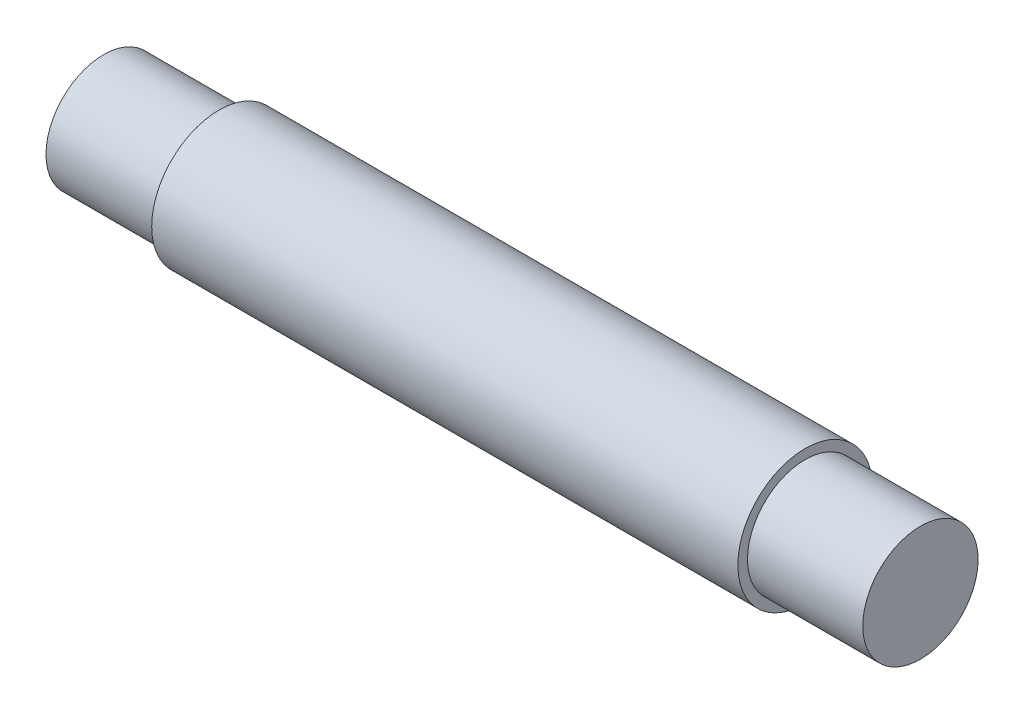
SolidWorks part; units mm, degrees
material "镀铬不锈钢"
ref_plane "前视基准面" through (0, 0, 0) normal (0, 0, 1) x (1, 0, 0)
ref_plane "上视基准面" through (0, 0, 0) normal (0, 1, 0) x (1, 0, 0)
ref_plane "右视基准面" through (0, 0, 0) normal (1, 0, 0) x (0, 0, -1)
sketch "草图1" plane through (0, 0, 0) normal (1, 0, 0) x (0, 0, -1)
  circle A0 centre (0, 0) radius 7
  dimension "D1" = 14
extrude "凸台-拉伸1" add sketch "草图1" along normal blind 85
sketch "草图2" plane through (0, 0, 0) normal (-1, 0, 0) x (0, 0, 1)
  circle A0 centre (0, 0) radius 6
  circle A1 centre (0, 0) radius 7.5
  dimension "D1" = 12
extrude "切除-拉伸1" cut sketch "草图2" against normal blind 12
cosmetic thread "装饰螺纹线2" parameters "D1"=10, "D2"=10.106
ref_plane "基准面1" through (42.5, 0, 0) normal (1, 0, 0) x (0, 0, -1)
mirror "镜向1" about plane through (42.5, 0, 0) normal (1, 0, 0) of "切除-拉伸1"
cosmetic thread "装饰螺纹线1" parameters "D1"=10, "D2"=10.106
